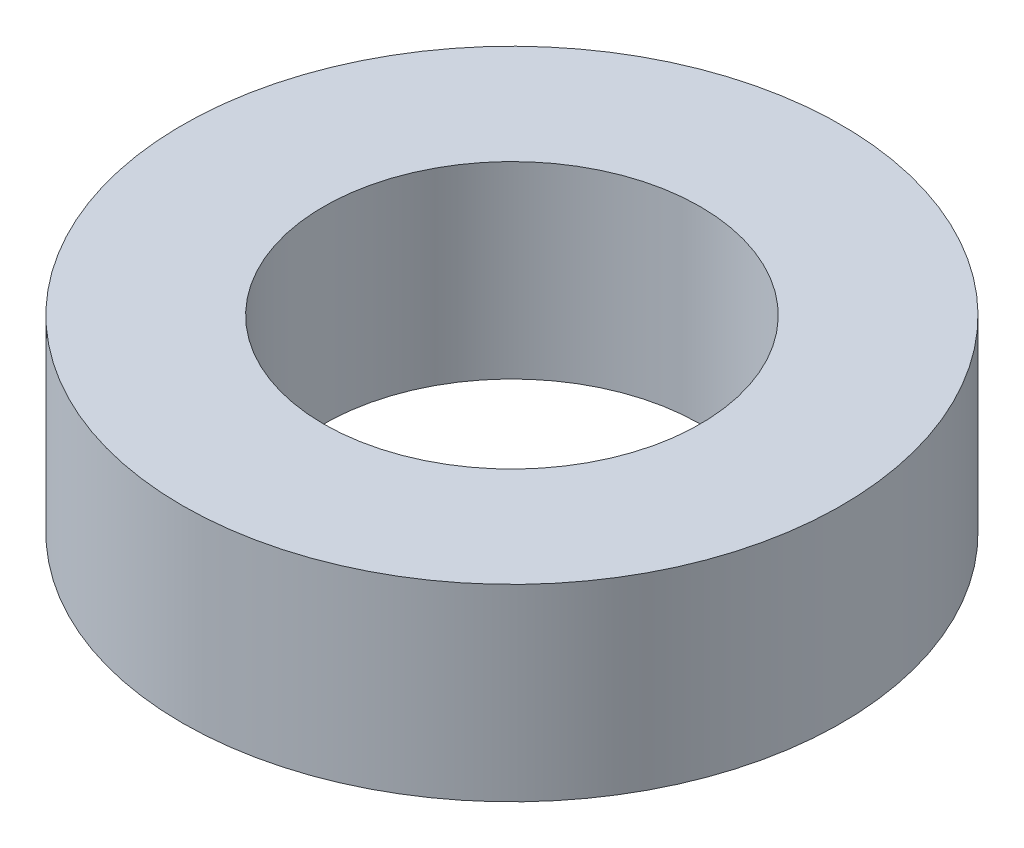
SolidWorks part; units mm, degrees
ref_plane "Front" through (0, 0, 0) normal (0, 0, 1) x (1, 0, 0)
ref_plane "Top" through (0, 0, 0) normal (0, 1, 0) x (1, 0, 0)
ref_plane "Right" through (0, 0, 0) normal (1, 0, 0) x (0, 0, -1)
sketch "Sketch1" plane through (0, 0, 0) normal (0, 1, 0) x (1, 0, 0)
  circle A0 centre (0, 0) radius 6.35
  circle A1 centre (0, 0) radius 11.1125
  dimension "D1" = 12.7
  dimension "D2" = 22.225
extrude "Boss-Extrude1" add sketch "Sketch1" along normal blind 6.35
